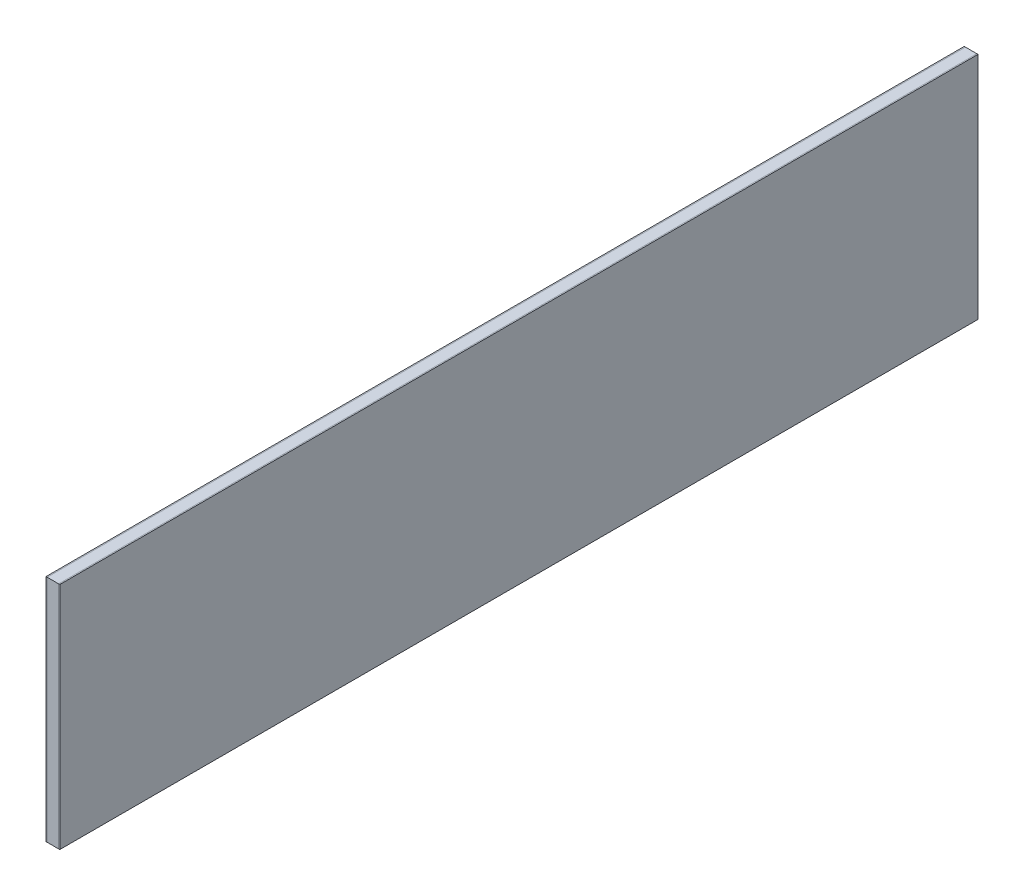
SolidWorks part; units mm, degrees
ref_plane "Front Plane" through (0, 0, 0) normal (0, 0, 1) x (1, 0, 0)
ref_plane "Top Plane" through (0, 0, 0) normal (0, 1, 0) x (1, 0, 0)
ref_plane "Right Plane" through (0, 0, 0) normal (1, 0, 0) x (0, 0, -1)
sketch "Sketch1" plane through (0, 0, 0) normal (1, 0, 0) x (0, 0, -1)
  line L1 (-100, 25) -> (100, 25)
  line L2 (-100, 25) -> (-100, -25)
  line L3 (-100, -25) -> (100, -25)
  line L4 (100, 25) -> (100, -25)
  point P0 (0, 0)
  point P6 (85, 0)
  dimension "D1" = 200
  dimension "D2" = 50
extrude "Boss-Extrude1" add sketch "Sketch1" along normal blind 0.25
sketch "Sketch2" plane through (0, 0, 0) normal (-1, 0, 0) x (0, 0, 1)
  line L4 (-100, 25) -> (-100, -25)
  line L5 (-100, 25) -> (-100, -25)
  line L6 (-100, -25) -> (100, -25)
  line L7 (-100, -25) -> (100, -25)
  line L12 (100, -25) -> (100, 25)
  line L13 (100, -25) -> (100, 25)
  line L14 (100, 25) -> (-100, 25)
  line L15 (100, 25) -> (-100, 25)
  dimension "D1" = 0
extrude "Boss-Extrude2" add sketch "Sketch2" along normal blind 2.5 separate body
sketch "Sketch3" plane through (-2.5, 0, 0) normal (-1, 0, 0) x (0, 0, 1)
  line L4 (100, 25) -> (-100, 25)
  line L5 (100, 25) -> (-100, 25)
  line L6 (-100, 25) -> (-100, -25)
  line L7 (-100, 25) -> (-100, -25)
  line L12 (-100, -25) -> (100, -25)
  line L13 (-100, -25) -> (100, -25)
  line L14 (100, -25) -> (100, 25)
  line L15 (100, -25) -> (100, 25)
  dimension "D1" = 0
extrude "Boss-Extrude3" add sketch "Sketch3" along normal blind 0.25 separate body
